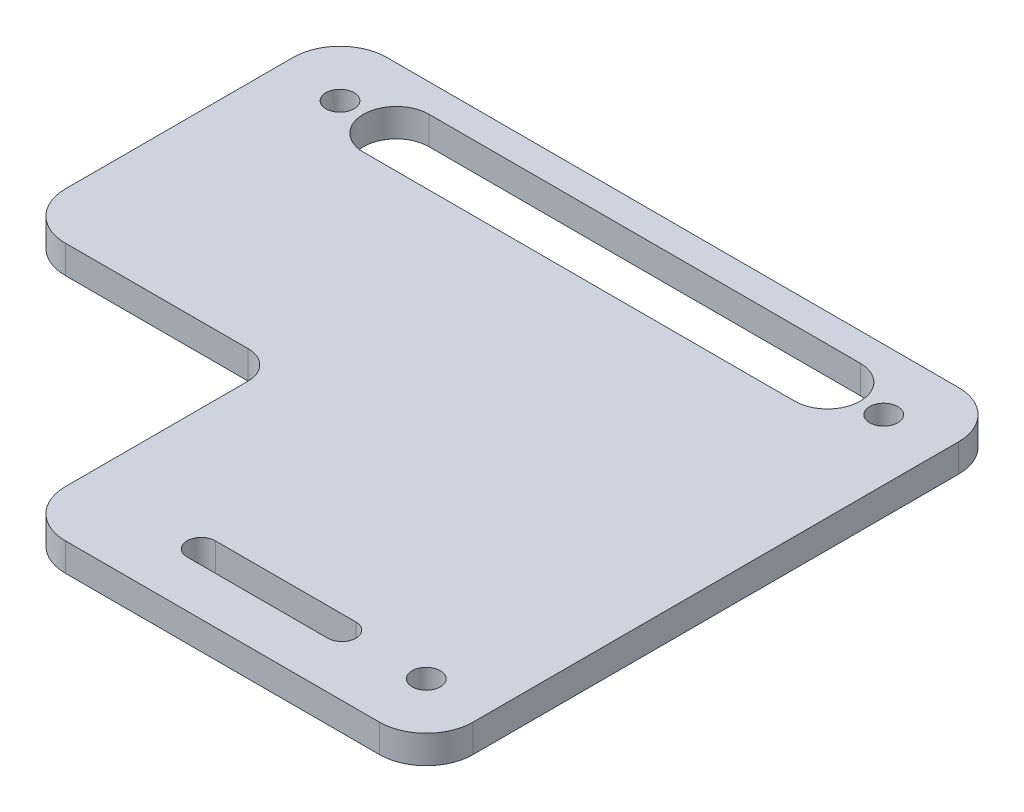
SolidWorks part; units mm, degrees
ref_plane "前视" through (0, 0, 0) normal (0, 0, 1) x (1, 0, 0)
ref_plane "上视" through (0, 0, 0) normal (0, 1, 0) x (1, 0, 0)
ref_plane "右视" through (0, 0, 0) normal (1, 0, 0) x (0, 0, -1)
sketch "草图1" plane through (0, 0, 0) normal (0, 1, 0) x (1, 0, 0)
  line L0 (-36.9075, 21.7379) -> (34.0925, 21.7379)
  line L1 (34.0925, 21.7379) -> (34.0925, -40.0621)
  line L2 (34.0925, -40.0621) -> (-36.9075, -40.0621)
  line L3 (-36.9075, -40.0621) -> (-36.9075, 21.7379)
  dimension "D1" = 71
  dimension "D2" = 61.8
extrude "凸台-拉伸1" add sketch "草图1" along normal blind 3
fillet "圆角1" radius 5 1 edges at (-36.9075, 1.5, -21.7379)
fillet "圆角3" radius 5 1 edges at (34.0925, 1.5, 40.0621)
fillet "圆角4" radius 5 1 edges at (34.0925, 1.5, -21.7379)
sketch "草图2" plane through (0, 0, 0) normal (0, -1, 0) x (-1, 0, 0)
  line L0 (36.9075, -40.0621) -> (-29.0925, -40.0621) construction
  line L1 (36.9075, 16.7379) -> (36.9075, -40.0621) construction
  line L2 (-34.0925, -35.0621) -> (-34.0925, 16.7379) construction
  line L4 (-29.0925, 21.7379) -> (31.9075, 21.7379) construction
  circle A1 centre (30.4075, 15.2379) radius 1.5
  circle A2 centre (-27.5925, -33.5621) radius 1.5
  circle A3 centre (-27.5925, 15.2379) radius 1.5
  dimension "D3" = 6.5
  dimension "D4" = 6.5
  dimension "D5" = 6.5
  dimension "D6" = 6.5
  dimension "D7" = 6.5
  dimension "D8" = 6.5
extrude "切除-拉伸1" cut sketch "草图2" against normal through all
sketch "草图5" plane through (0, 0, 0) normal (0, -1, 0) x (-1, 0, 0)
  line L0 (1.4075, 13.5905) -> (1.4075, 17.5407) construction
  line L1 (36.9075, 16.7379) -> (36.9075, -40.0621) construction
  line L2 (-27.5925, 15.2379) -> (30.4075, 15.2379) construction
  line L3 (24.4075, 15.2379) -> (-21.5925, 15.2379) construction
  line L4 (24.4075, 11.7379) -> (-21.5925, 11.7379)
  line L5 (24.4075, 18.7379) -> (-21.5925, 18.7379)
  arc A0 (24.4075, 11.7379) -> (24.4075, 18.7379) centre (24.4075, 15.2379) ccw
  arc A1 (-21.5925, 18.7379) -> (-21.5925, 11.7379) centre (-21.5925, 15.2379) ccw
  point P10 (1.4075, 15.2379)
  dimension "D1" = 35.5
extrude "切除-拉伸2" cut sketch "草图5" against normal through all
sketch "草图6" plane through (0, 0, 0) normal (0, -1, 0) x (1, 0, 0)
  line L0 (-36.9075, 40.0621) -> (-9.4075, 40.0621)
  line L1 (-36.9075, 40.0621) -> (29.0925, 40.0621) construction
  line L2 (-9.4075, 40.0621) -> (-9.4075, 12.5621)
  line L3 (-9.4075, 12.5621) -> (-36.9075, 12.5621)
  line L4 (-36.9075, -16.7379) -> (-36.9075, 40.0621) construction
  line L5 (-36.9075, 12.5621) -> (-36.9075, 40.0621)
  dimension "D1" = 27.5
  dimension "D2" = 27.5
extrude "切除-拉伸3" cut sketch "草图6" against normal through all
fillet "圆角5" radius 5 2 edges at (-36.9075, 1.5, 12.5621) (-9.4075, 1.5, 40.0621)
fillet "圆角6" radius 3 1 edges at (-9.4075, 1.5, 12.5621)
sketch "草图7" plane through (0, 0, 0) normal (0, -1, 0) x (1, 0, 0)
  line L0 (27.5925, 33.5621) -> (-5.4075, 33.5621) construction
  line L1 (3.5925, 33.5621) -> (18.5925, 33.5621) construction
  line L2 (3.5925, 35.0621) -> (18.5925, 35.0621)
  line L3 (3.5925, 32.0621) -> (18.5925, 32.0621)
  line L4 (34.0925, 35.0621) -> (34.0925, -16.7379) construction
  arc A0 (3.5925, 35.0621) -> (3.5925, 32.0621) centre (3.5925, 33.5621) ccw
  arc A1 (18.5925, 32.0621) -> (18.5925, 35.0621) centre (18.5925, 33.5621) ccw
  point P5 (11.0925, 33.5621)
  dimension "D1" = 23
extrude "切除-拉伸4" cut sketch "草图7" against normal through all
